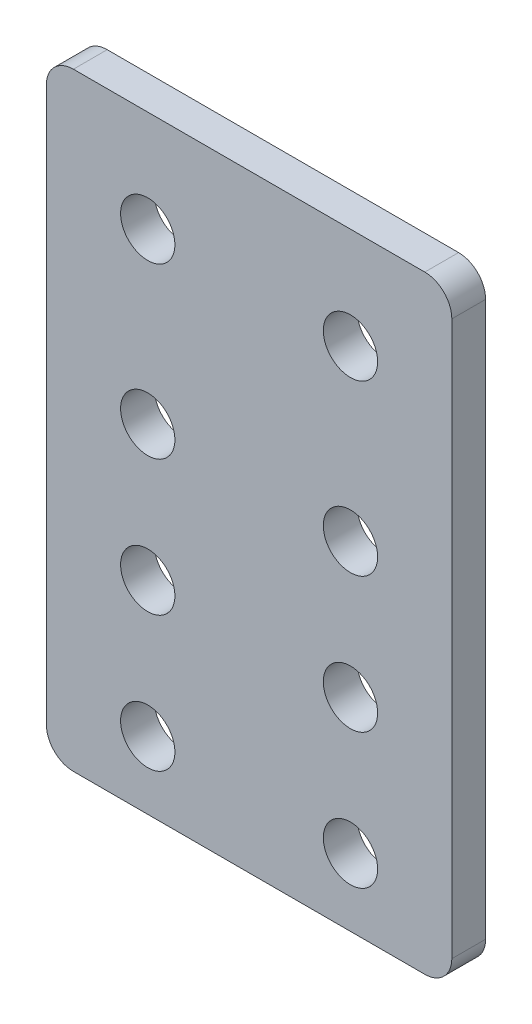
SolidWorks part; units mm, degrees
material "6061-T6 (SS)"
ref_plane "Front Plane" through (0, 0, 0) normal (0, 0, 1) x (1, 0, 0)
ref_plane "Top Plane" through (0, 0, 0) normal (0, 1, 0) x (1, 0, 0)
ref_plane "Right Plane" through (0, 0, 0) normal (1, 0, 0) x (0, 0, -1)
sketch "Sketch1" plane through (0, 0, 0) normal (0, 0, 1) x (1, 0, 0)
  line L5 (-19.05, -28.575) -> (19.05, -28.575)
  line L6 (-19.05, -28.575) -> (-19.05, 28.575)
  line L11 (-19.05, 28.575) -> (19.05, 28.575)
  line L15 (19.05, -28.575) -> (19.05, 28.575)
  line L16 (-19.05, -28.575) -> (19.05, 28.575) construction
  line L17 (-19.05, 28.575) -> (19.05, -28.575) construction
  line L18 (0, 28.575) -> (0, -28.575) construction
  circle A15 centre (-9.525, 3.175) radius 2.5527
  circle A16 centre (-9.525, 19.05) radius 2.5527
  circle A19 centre (9.525, 3.175) radius 2.5527
  circle A20 centre (9.525, 19.05) radius 2.5527
  circle A22 centre (-9.525, -9.525) radius 2.5527
  circle A23 centre (9.525, -9.525) radius 2.5527
  circle A24 centre (-9.525, -22.225) radius 2.5527
  circle A25 centre (9.525, -22.225) radius 2.5527
  point P0 (0, 0)
  point P16 (0, 0)
  point P27 (0, 0)
  point P28 (-10.5021, -7.9224)
  point P29 (0, 0)
  point P30 (9.525, 20.6375)
  point P31 (0, 0)
  point P32 (-9.525, 20.6375)
  dimension "D4" = 9.525
  dimension "D5" = 19.05
  dimension "D7" = 5.1054
  dimension "D1" = 6.35
  dimension "D6" = 38.1
  dimension "D8" = 12.7
  dimension "D9" = 15.875
  dimension ".5" = 12.7
extrude "Boss-Extrude1" add sketch "Sketch1" along normal blind 3.175
fillet "Fillet1" radius 2.54 4 edges at (-19.05, 28.575, 1.5875) (-19.05, -28.575, 1.5875) (19.05, -28.575, 1.5875) (19.05, 28.575, 1.5875)
